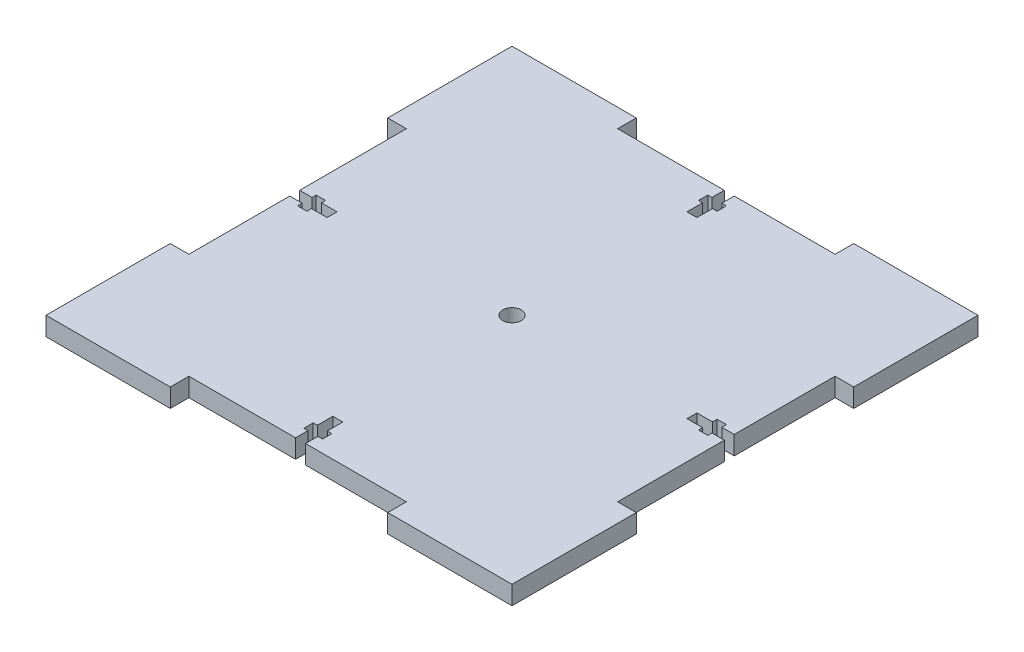
SolidWorks part; units mm, degrees
ref_plane "Front Plane" through (0, 0, 0) normal (0, 0, 1) x (1, 0, 0)
ref_plane "Top Plane" through (0, 0, 0) normal (0, 1, 0) x (1, 0, 0)
ref_plane "Right Plane" through (0, 0, 0) normal (1, 0, 0) x (0, 0, -1)
sketch "Sketch1" plane through (0, 0, 0) normal (0, 1, 0) x (1, 0, 0)
  line L0 (69, -35) -> (69, 35)
  line L1 (-75, -75) -> (75, -75)
  line L2 (-75, -75) -> (-75, 75)
  line L3 (-75, 75) -> (75, 75)
  line L4 (75, -75) -> (75, 75)
  line L5 (-75, -75) -> (75, 75) construction
  line L6 (-75, 75) -> (75, -75) construction
  line L7 (-35, 75) -> (35, 75)
  line L8 (-35, 75) -> (-35, 69)
  line L9 (-35, 69) -> (35, 69)
  line L10 (35, 75) -> (35, 69)
  line L11 (75, 35) -> (69, 35)
  line L12 (75, -35) -> (75, 35)
  line L13 (75, -35) -> (69, -35)
  line L14 (-69, 35) -> (-69, -35)
  line L15 (-75, -35) -> (-69, -35)
  line L16 (-75, 35) -> (-75, -35)
  line L17 (-75, 35) -> (-69, 35)
  line L18 (-99.8667, 0) -> (108.8889, 0) construction
  line L19 (-35, -69) -> (35, -69)
  line L20 (35, -75) -> (35, -69)
  line L21 (-35, -75) -> (35, -75)
  line L22 (-35, -75) -> (-35, -69)
  line L23 (-62, 1.9838) -> (-62, -4.0168)
  line L24 (-0.6616, 69) -> (2.5384, 69)
  line L25 (-0.6616, 69) -> (-0.6616, 57)
  line L30 (-0.6616, 57) -> (2.5384, 57)
  line L31 (2.5384, 69) -> (2.5384, 57)
  line L32 (-1.9838, 65) -> (4.0168, 65)
  line L33 (-1.9838, 65) -> (-1.9838, 62)
  line L34 (-1.9838, 62) -> (4.0168, 62)
  line L35 (4.0168, 65) -> (4.0168, 62)
  line L36 (-65, -4.0168) -> (-62, -4.0168)
  line L37 (-65, 1.9838) -> (-65, -4.0168)
  line L38 (-65, 1.9838) -> (-62, 1.9838)
  line L39 (-57, 0.6616) -> (-57, -2.5384)
  line L40 (-69, -2.5384) -> (-57, -2.5384)
  line L41 (-69, 0.6616) -> (-69, -2.5384)
  line L42 (-69, 0.6616) -> (-57, 0.6616)
  line L43 (62, -1.9838) -> (62, 4.0168)
  line L44 (65, 4.0168) -> (62, 4.0168)
  line L45 (65, -1.9838) -> (65, 4.0168)
  line L46 (65, -1.9838) -> (62, -1.9838)
  line L47 (57, -0.6616) -> (57, 2.5384)
  line L48 (69, 2.5384) -> (57, 2.5384)
  line L49 (69, -0.6616) -> (69, 2.5384)
  line L50 (69, -0.6616) -> (57, -0.6616)
  line L51 (-1.9838, -62) -> (4.0168, -62)
  line L52 (4.0168, -65) -> (4.0168, -62)
  line L53 (-1.9838, -65) -> (4.0168, -65)
  line L54 (-1.9838, -65) -> (-1.9838, -62)
  line L55 (-0.6616, -57) -> (2.5384, -57)
  line L56 (2.5384, -69) -> (2.5384, -57)
  line L57 (-0.6616, -69) -> (2.5384, -69)
  line L58 (-0.6616, -69) -> (-0.6616, -57)
  circle A0 centre (0, 0) radius 3
  point P0 (0, 0)
  dimension "D6" = 6
  dimension "D1" = 150
  dimension "D2" = 150
  dimension "D3" = 6
  dimension "D4" = 40
  dimension "D5" = 40
  dimension "D7" = 3.2
  dimension "D8" = 12
  dimension "D9" = 3
  dimension "D10" = 1.4784
  dimension "D11" = 4
  dimension "D12" = 72.4616
  dimension "D13" = 74.3384
extrude "Boss-Extrude1" add sketch "Sketch1" along normal blind 6 contours L1 L22 L19 L20 L4 L13 L0 L11 L3 L10 L9 L8 L2 L17 L14 L15
